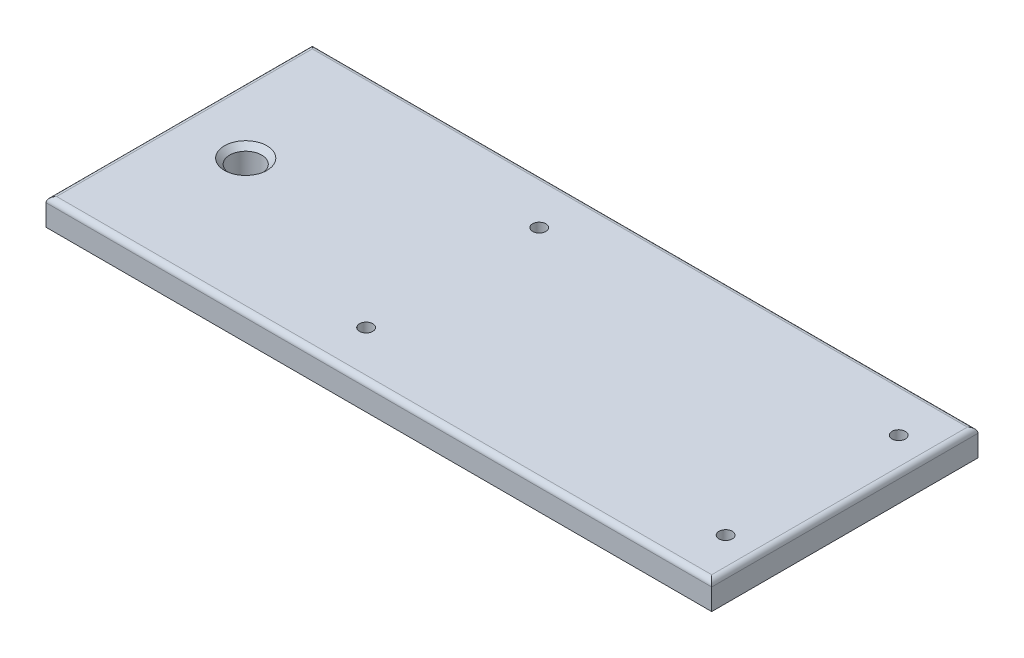
SolidWorks part; units mm, degrees
ref_plane "Front Plane" through (0, 0, 0) normal (0, 0, 1) x (1, 0, 0)
ref_plane "Top Plane" through (0, 0, 0) normal (0, 1, 0) x (1, 0, 0)
ref_plane "Right Plane" through (0, 0, 0) normal (1, 0, 0) x (0, 0, -1)
sketch "Sketch1" plane through (0, 0, 0) normal (0, 1, 0) x (1, 0, 0)
  line L1 (125, -50) -> (-125, -50)
  line L2 (125, -50) -> (125, 50)
  line L3 (125, 50) -> (-125, 50)
  line L4 (-125, -50) -> (-125, 50)
  line L5 (0, 50) -> (0, -50) construction
  line L6 (125, 0) -> (-125, 0) construction
  point P0 (0, 0)
  dimension "D1" = 250
  dimension "D2" = 100
extrude "Boss-Extrude1" add sketch "Sketch1" along normal blind 10
fillet "Fillet1" radius 2 4 edges at (-125, 10, 0) (0, 10, -50) (125, 10, 0) (0, 10, 50)
sketch "Sketch2" plane through (0, 10, 0) normal (0, 1, 0) x (1, 0, 0)
  line L0 (-125, -50) -> (-125, 50) construction
  circle A0 centre (-100, 0) radius 6
  dimension "D2" = 12
  dimension "D1" = 25
extrude "Cut-Extrude1" cut sketch "Sketch2" against normal through all
chamfer "Chamfer1" distance 2 angle 45 1 edges at (-100, 10, 6)
sketch "Sketch3" plane through (0, 10, 0) normal (0, 1, 0) x (1, 0, 0)
  circle A0 centre (112.7238, 32.5) radius 2.5
  circle A1 centre (112.7238, -32.5) radius 2.5
  circle A2 centre (-22.2762, 32.5) radius 2.5
  circle A3 centre (-22.2762, -32.5) radius 2.5
  dimension "D1" = 5
extrude "Cut-Extrude2" cut sketch "Sketch3" against normal through all
